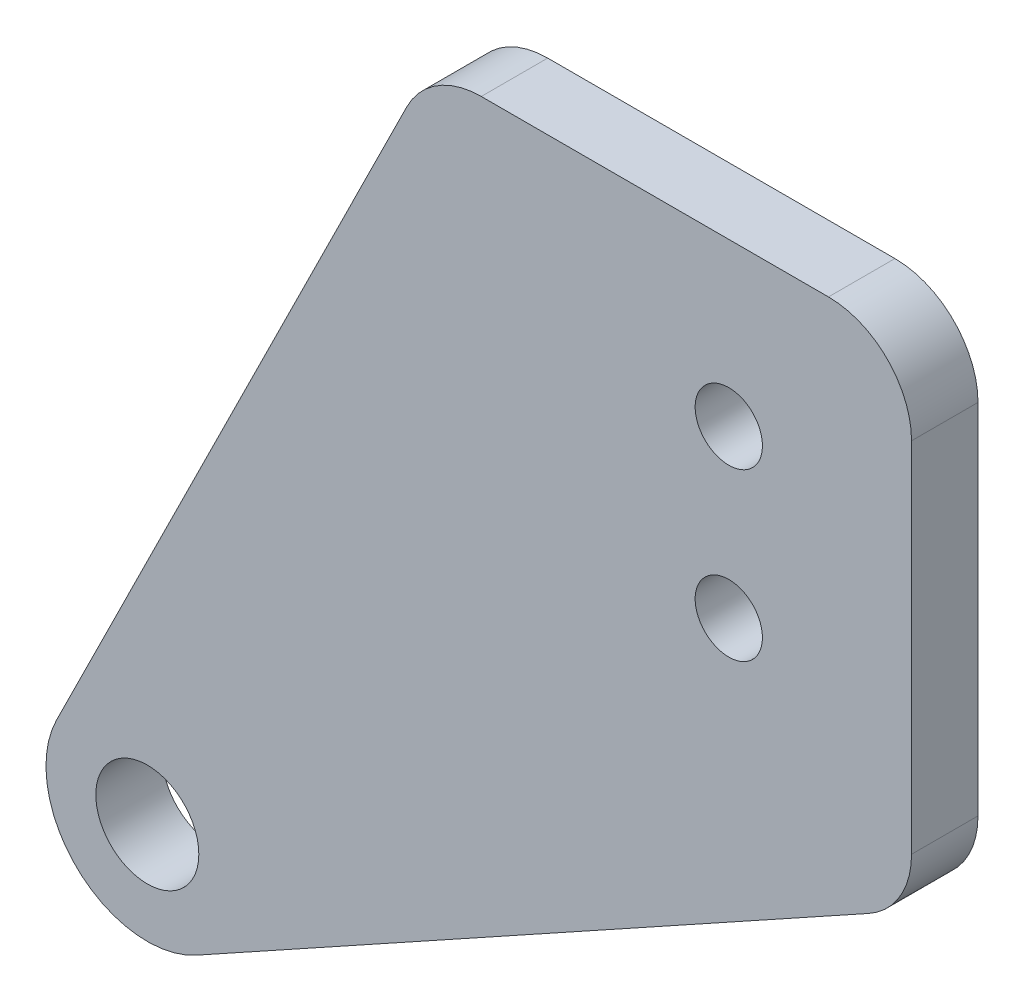
SolidWorks part; units mm, degrees
material "Thornel Mat VMA"
ref_plane "前视基准面" through (0, 0, 0) normal (0, 0, 1) x (1, 0, 0)
ref_plane "上视基准面" through (0, 0, 0) normal (0, 1, 0) x (1, 0, 0)
ref_plane "右视基准面" through (0, 0, 0) normal (1, 0, 0) x (0, 0, -1)
other "Configuration Table"
sketch "草图2" plane through (0, 0, 0) normal (0, 0, 1) x (1, 0, 0)
  line L0 (0, 0) -> (50000, 0) construction
  line L1 (-4, -5) -> (4, -5) construction
  line L2 (-4, -5) -> (-4, 5) construction
  line L3 (-4, 5) -> (4, 5) construction
  line L4 (4, -5) -> (4, 5) construction
  line L5 (-4, -5) -> (4, 5) construction
  line L6 (-4, 5) -> (4, -5) construction
  line L7 (-22, 14.75) -> (-44.4647, -30.5394)
  line L8 (-22, -14.75) -> (7, -14.75)
  line L9 (-22, -14.75) -> (-22, 14.75)
  line L10 (-22, 14.75) -> (7, 14.75)
  line L11 (7, -14.75) -> (7, 14.75)
  line L12 (-22, -14.75) -> (7, 14.75) construction
  line L13 (-22, 14.75) -> (7, -14.75) construction
  line L14 (-36.0449, -38.5864) -> (7, -14.75)
  circle A0 centre (-4, 5) radius 2.025
  circle A3 centre (-4, -5) radius 2.025
  arc A4 (-44.4647, -30.5394) -> (-36.0449, -38.5864) centre (-39, -33.25) ccw
  circle A5 centre (-39, -33.25) radius 3.1
  point P0 (0, 0)
  point P12 (-7.5, 0)
  dimension "D3" = 4.05
  dimension "D7" = 3
  dimension "D8" = 6.2
  dimension "D1" = 8
  dimension "D2" = 10
  dimension "D4" = 18
  dimension "D5" = 29.5
  dimension "D6" = 3
  dimension "D9" = 48
  dimension "D10" = 17
extrude "凸台-拉伸1" add sketch "草图2" along normal blind 4
fillet "圆角1" radius 5 3 edges at (7, 14.75, 2) (7, -14.75, 2) (-22, 14.75, 2)
sketch "草图3" plane through (0, 0, 4) normal (0, 0, 1) x (1, 0, 0)
  circle A0 centre (-39, -33.25) radius 10
  dimension "D1" = 20
